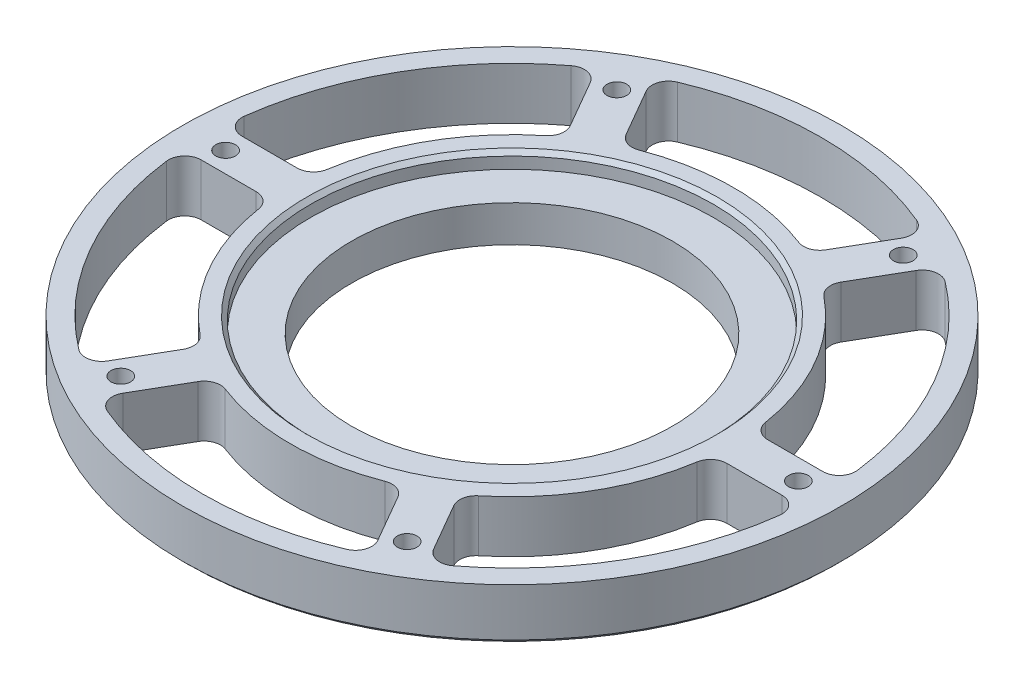
SolidWorks part; units mm, degrees
material "6061-T6 (SS)"
ref_plane "Front Plane" through (0, 0, 0) normal (0, 0, 1) x (1, 0, 0)
ref_plane "Top Plane" through (0, 0, 0) normal (0, 1, 0) x (1, 0, 0)
ref_plane "Right Plane" through (0, 0, 0) normal (1, 0, 0) x (0, 0, -1)
sketch "Sketch2" plane through (0, 0, 0) normal (1, 0, 0) x (0, 0, -1)
  line L0 (-39.2125, 0) -> (-80.55, 0)
  line L1 (-80.55, 0) -> (-80.55, 12.7)
  line L2 (-80.55, 12.7) -> (-49.2125, 12.7)
  line L3 (-49.2125, 12.7) -> (-49.2125, 8.9)
  line L4 (-49.2125, 8.9) -> (-39.2125, 8.9)
  line L5 (-39.2125, 8.9) -> (-39.2125, 0)
  dimension "D1" = 80.55
  dimension "D2" = 12.7
  dimension "D4" = 49.2125
  dimension "D5" = 10
  dimension "D3" = 8.9
ref_axis "Axis1" through (0, -0.635, 0) along (0, 1, 0)
revolve "Revolve1" add sketch "Sketch2" angle 360 about axis through (0, -0.635, 0) along (0, 1, 0)
hole_wizard "#12 (0.189) Diameter Hole1" positions "Sketch6" profile "Sketch7" hole size "#12" standard "ANSI Inch" end condition through all
sketch "Sketch6" plane through (0, 12.7, 0) normal (0, 1, 0) x (1, 0, 0)
  line L0 (0, 0) -> (-69.8201, 120.932) construction
  line L2 (0, 0) -> (0, 109.0908) construction
  point P0 (-35, 60.6218)
  dimension "D1" = 30
  dimension "D2" = 70
sketch "Sketch7" plane through (-35, 12.7, -60.6218) normal (1, 0, 0) x (0, 0, 1)
  line L0 (0, 0) -> (0, 12.7)
  line L1 (0, 12.7) -> (2.4003, 12.7)
  line L2 (2.4003, 12.7) -> (2.4003, 0)
  line L5 (2.4003, 0) -> (0, 0)
  line L11 (0, -6.35) -> (0, 107.95) construction
  dimension "Thru Hole Dia." = 4.8006
  dimension "Thru Hole Depth" = 12.7
pattern_circular "CirPattern3" count 6 over 360 about axis through (0, 0, 0) along (0, 1, 0) of "#12 (0.189) Diameter Hole1"
sketch "Sketch8" plane through (0, 12.7, 0) normal (0, 1, 0) x (1, 0, 0)
  line L0 (-33.3621, 67.7848) -> (-22.6606, 49.2493)
  line L1 (33.3621, 67.7848) -> (22.6606, 49.2493)
  line L2 (0, 0) -> (-35, 60.6218) construction
  line L4 (0, 0) -> (0, 93.9995) construction
  arc A0 (-22.6606, 49.2493) -> (22.6606, 49.2493) centre (0, 0) cw
  arc A1 (-33.3621, 67.7848) -> (33.3621, 67.7848) centre (0, 0) cw
  circle A2 centre (0, 0) radius 49.2125 construction
  circle A3 centre (0, 0) radius 80.55 construction
  dimension "D1" = 5
  dimension "D2" = 5
  dimension "D3" = 5
extrude "Cut-Extrude1" cut sketch "Sketch8" against normal through all
fillet "Fillet1" radius 4 4 edges at (33.3621, 6.35, -67.7848) (22.6606, 6.35, -49.2493) (-33.3621, 6.35, -67.7848) (-22.6606, 6.35, -49.2493)
pattern_circular "CirPattern4" count 6 over 360 about axis through (0, 0, 0) along (0, 1, 0) of "Cut-Extrude1", "Fillet1"
chamfer "Chamfer1" distance 1 angle 45 1 edges at (0, 12.7, -49.2125)
chamfer "Chamfer2" distance 1 angle 45 1 edges at (0, 0, -80.55)
equation "\"TubeDiameter\" = 6.500in"
equation "\"D1@Sketch2\"=(\"TubeDiameter\"-4)/2"
